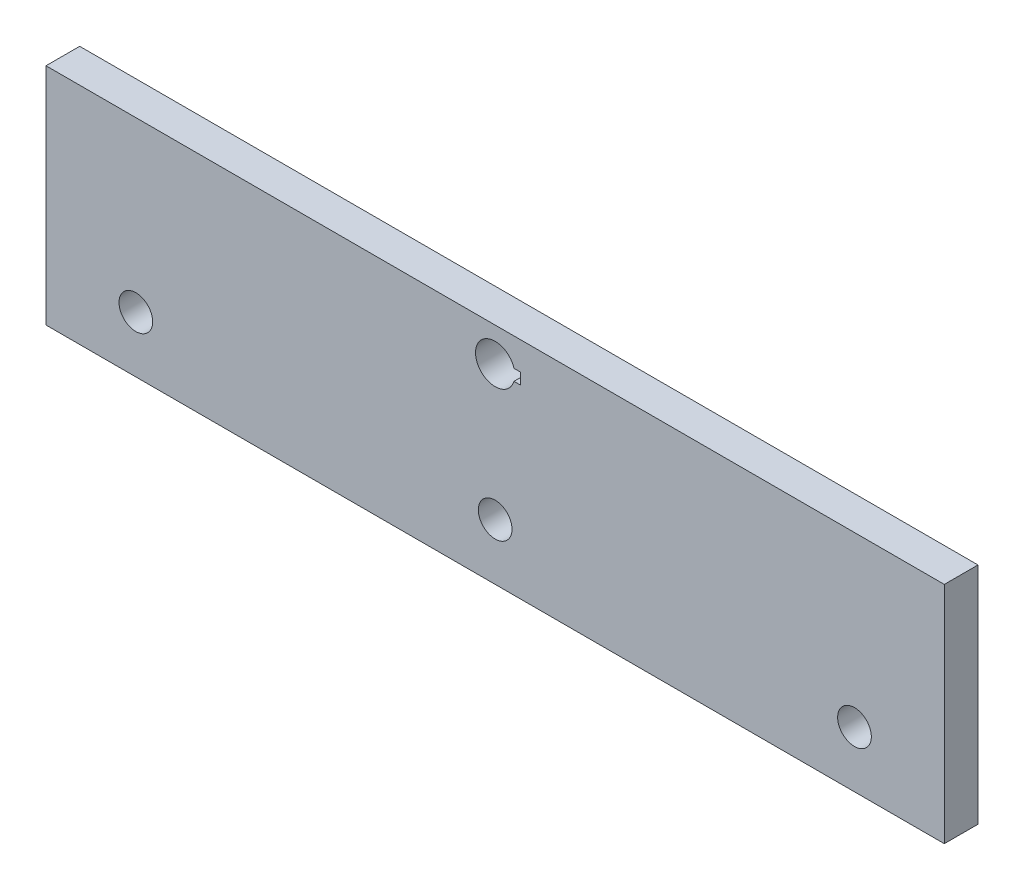
SolidWorks part; units mm, degrees
ref_plane "Front Plane" through (0, 0, 0) normal (0, 0, 1) x (1, 0, 0)
ref_plane "Top Plane" through (0, 0, 0) normal (0, 1, 0) x (1, 0, 0)
ref_plane "Right Plane" through (0, 0, 0) normal (1, 0, 0) x (0, 0, -1)
sketch "Sketch1" plane through (0, 0, 0) normal (0, 0, 1) x (1, 0, 0)
  line L1 (0, 0) -> (80, 0)
  line L2 (0, 0) -> (0, 20)
  line L3 (0, 20) -> (80, 20)
  line L4 (80, 0) -> (80, 20)
  dimension "D1" = 80
  dimension "D2" = 20
extrude "Boss-Extrude1" add sketch "Sketch1" along normal blind 3
extrude "Cut-Extrude1" cut sketch "Sketch2" against normal blind 6
sketch "Sketch2" plane through (88.7727, -6.4689, 0) normal (0, 0, -1) x (-1, 0, 0)
  line L0 (8.7727, 11.4689) -> (88.7727, 11.4689) construction
  circle A0 centre (16.7727, 11.4689) radius 1.5
  circle A1 centre (48.7727, 11.4689) radius 1.5
  circle A2 centre (80.7727, 11.4689) radius 1.5
  point P13 (48.7727, 11.4689)
extrude "Cut-Extrude2" cut sketch "Sketch3" against normal blind 3
sketch "Sketch3" plane through (88.7727, -6.4689, 0) normal (0, 0, -1) x (-1, 0, 0)
  line L3 (46.5227, 23.9689) -> (47.0956, 23.9689)
  line L4 (46.5227, 22.9689) -> (46.5227, 23.9689)
  line L5 (47.0956, 22.9689) -> (46.5227, 22.9689)
  arc A1 (47.0956, 22.9689) -> (47.0956, 23.9689) centre (48.7727, 23.4689) ccw
